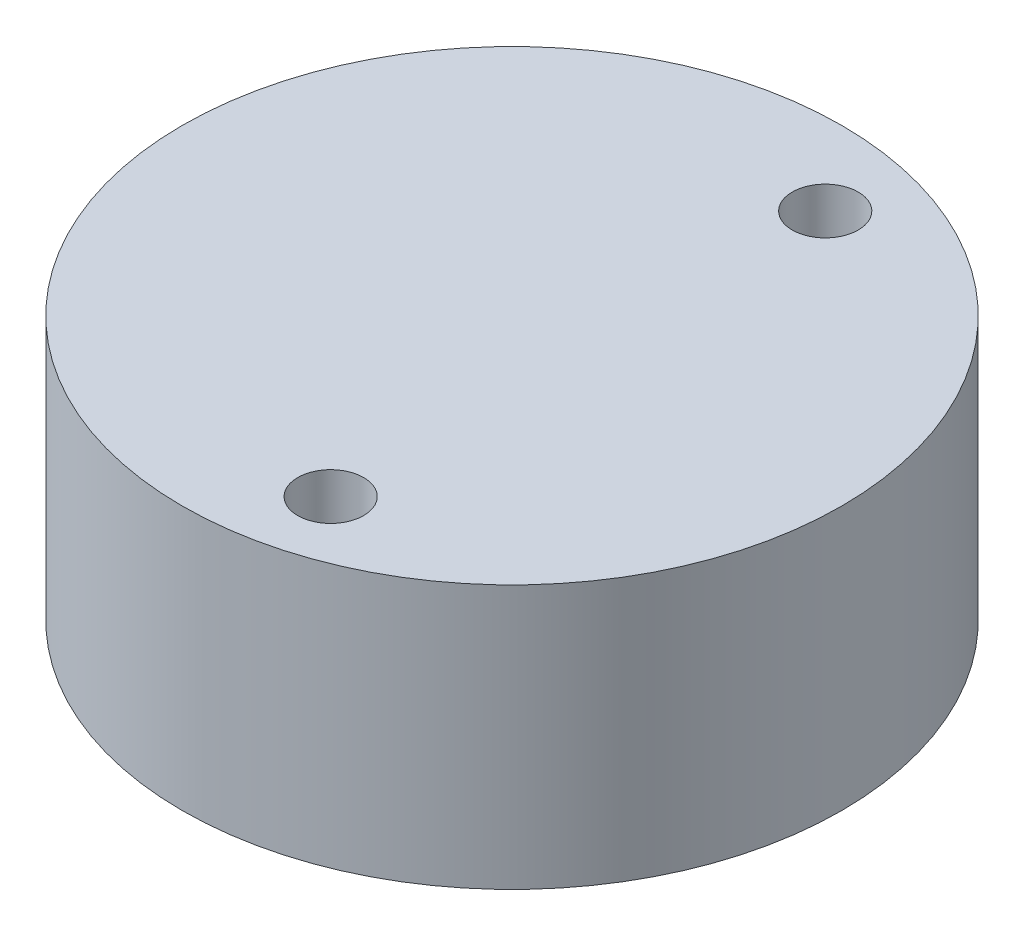
SolidWorks part; units mm, degrees
ref_plane "Front Plane" through (0, 0, 0) normal (0, 0, 1) x (1, 0, 0)
ref_plane "Top Plane" through (0, 0, 0) normal (0, 1, 0) x (1, 0, 0)
ref_plane "Right Plane" through (0, 0, 0) normal (1, 0, 0) x (0, 0, -1)
sketch "Sketch1" plane through (0, 0, 0) normal (0, 1, 0) x (1, 0, 0)
  line L0 (-1, 0) -> (0, 0) construction
  circle A0 centre (0, 0) radius 3
  circle A1 centre (-1, 0) radius 5
  dimension "D1" = 6
  dimension "D2" = 10
  dimension "D3" = 1
extrude "Boss-Extrude1" add sketch "Sketch1" along normal blind 2
sketch "Sketch2" plane through (0, 2, 0) normal (0, 1, 0) x (1, 0, 0)
  circle A0 centre (-1, 0) radius 5
  circle A1 centre (-1, 0) radius 5 construction
extrude "Boss-Extrude2" add sketch "Sketch2" along normal blind 2
sketch "Sketch3" plane through (0, 0, 0) normal (0, -1, 0) x (1, 0, 0)
  line L0 (0, 3.75) -> (0, -3.75) construction
  circle A0 centre (0, 3.75) radius 0.5
  circle A1 centre (0, -3.75) radius 0.5
  point P4 (0, 0)
  dimension "D2" = 1
  dimension "D3" = 1
  dimension "D1" = 0
  dimension "D4" = 7.5
extrude "Cut-Extrude1" cut sketch "Sketch3" against normal through all
sketch "Sketch4" plane through (0, 0, 0) normal (0, -1, 0) x (1, 0, 0)
  line L0 (-2, -2.2361) -> (-2, 2.2361)
  line L2 (-2, -2.2361) -> (-2, 2.2361) construction
  circle A0 centre (0, 0) radius 3
  circle M5 centre (0, 0) radius 3
extrude "Boss-Extrude3" add sketch "Sketch4" against normal blind 4 contours L0 M5
